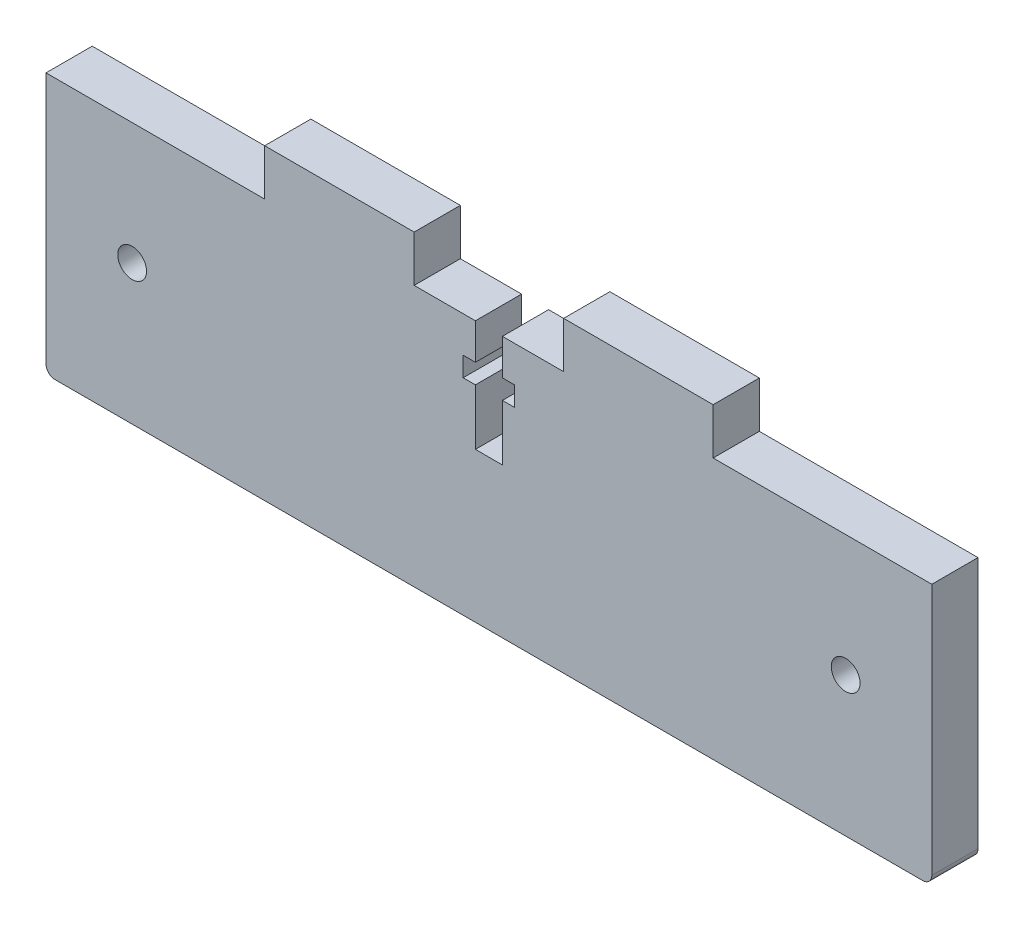
SolidWorks part; units mm, degrees
ref_plane "Front Plane" through (0, 0, 0) normal (0, 0, 1) x (1, 0, 0)
ref_plane "Top Plane" through (0, 0, 0) normal (0, 1, 0) x (1, 0, 0)
ref_plane "Right Plane" through (0, 0, 0) normal (1, 0, 0) x (0, 0, -1)
sketch "Sketch1" plane through (0, 0, 0) normal (0, 0, 1) x (1, 0, 0)
  line L1 (-54.0961, 17.4963) -> (44.2639, 17.4963)
  line L2 (-54.0961, 17.4963) -> (-54.0961, -10.5037)
  line L3 (-53.0961, -11.5037) -> (43.2639, -11.5037)
  line L4 (44.2639, 17.4963) -> (44.2639, -10.5037)
  arc A0 (43.2639, -11.5037) -> (44.2639, -10.5037) centre (43.2639, -10.5037) ccw
  arc A1 (-53.0961, -11.5037) -> (-54.0961, -10.5037) centre (-53.0961, -10.5037) cw
  point P6 (44.2639, -11.5037)
  dimension "D3" = 1
  dimension "D1" = 98.36
  dimension "D2" = 29
extrude "Main" add sketch "Sketch1" along normal blind 5.13
hole_wizard "M3 Clearance Hole1" positions "Sketch3" profile "Sketch2" hole size "M3" standard "Ansi Metric" end condition up to next
sketch "Sketch3" plane through (0, 0, 5.13) normal (0, 0, 1) x (1, 0, 0)
  line L1 (-54.0961, 17.4963) -> (-54.0961, -10.5037) construction
  line L2 (-53.0961, -11.5037) -> (43.2639, -11.5037) construction
  line L3 (44.2639, -10.5037) -> (44.2639, 17.4963) construction
  point P0 (-44.5301, 3.9963)
  point P1 (34.6979, 3.9963)
  point P8 (44.2639, 3.4963)
  dimension "D1" = 9.566
  dimension "D2" = 15.5
  dimension "D3" = 9.566
  dimension "D4" = 15.5
sketch "Sketch2" plane through (-44.5301, 3.9963, 5.13) normal (1, 0, 0) x (0, -1, 0)
  line L0 (0, 0) -> (0, 5.13)
  line L1 (0, 5.13) -> (1.6, 5.13)
  line L2 (1.6, 5.13) -> (1.6, 0)
  line L5 (1.6, 0) -> (0, 0)
  line L11 (0, -6.35) -> (0, 107.95) construction
  dimension "Thru Hole Dia." = 3.2
  dimension "Thru Hole Depth" = 5.13
sketch "Sketch4" plane through (0, 17.4963, 0) normal (0, 1, 0) x (1, 0, 0)
  line L0 (44.2639, 0) -> (-54.0961, 0) construction
  line L1 (19.9839, 0) -> (3.3839, 0)
  line L2 (19.9839, 0) -> (19.9839, -5.13)
  line L3 (19.9839, -5.13) -> (3.3839, -5.13)
  line L4 (3.3839, 0) -> (3.3839, -5.13)
  line L5 (44.2639, -5.13) -> (-54.0961, -5.13) construction
  line L6 (-13.2161, 0) -> (-29.8161, 0)
  line L7 (-13.2161, 0) -> (-13.2161, -5.13)
  line L8 (-13.2161, -5.13) -> (-29.8161, -5.13)
  line L9 (-29.8161, 0) -> (-29.8161, -5.13)
  line L10 (44.2639, -5.13) -> (44.2639, 0) construction
  dimension "D1" = 16.6
  dimension "D3" = 49.8
  dimension "D4" = 24.28
  dimension "D2" = 2
extrude "top tabs" add sketch "Sketch4" along normal blind 5.13
sketch "Sketch5" plane through (0, 0, 5.13) normal (0, 0, 1) x (1, 0, 0)
  line L0 (-6.4146, 17.4963) -> (-6.4146, 13.5013)
  line L1 (-3.4176, 13.5013) -> (-3.4176, 17.4963)
  line L2 (-2.0586, 13.5013) -> (-3.4176, 13.5013)
  line L3 (-3.4176, 11.3343) -> (-2.0586, 11.3343)
  line L4 (-2.0586, 11.3343) -> (-2.0586, 13.5013)
  line L5 (-6.4146, 13.5013) -> (-7.7736, 13.5013)
  line L6 (-7.7736, 11.3343) -> (-6.4146, 11.3343)
  line L7 (-7.7736, 13.5013) -> (-7.7736, 11.3343)
  line L8 (-6.4146, 5.1273) -> (-3.4176, 5.1273)
  line L9 (-3.4176, 5.1273) -> (-3.4176, 11.3343)
  line L10 (-6.4146, 11.3343) -> (-6.4146, 5.1273)
  line L11 (44.2639, -10.5037) -> (44.2639, 17.4963) construction
  dimension "D1" = 2.997
  dimension "D2" = 47.6815
extrude "t-slot" cut sketch "Sketch5" against normal through all and the other way through all
equation "\"D3@Sketch3\" = \"D1@Sketch3\""
equation "\"D4@Sketch3\" = \"D2@Sketch3\""
equation "\"D4@Sketch4\" = (\"D1@Sketch1\"-\"D3@Sketch4\")/2"
equation "\"D2@Sketch5\" = (\"D1@Sketch1\"-\"D1@Sketch5\")/2"
